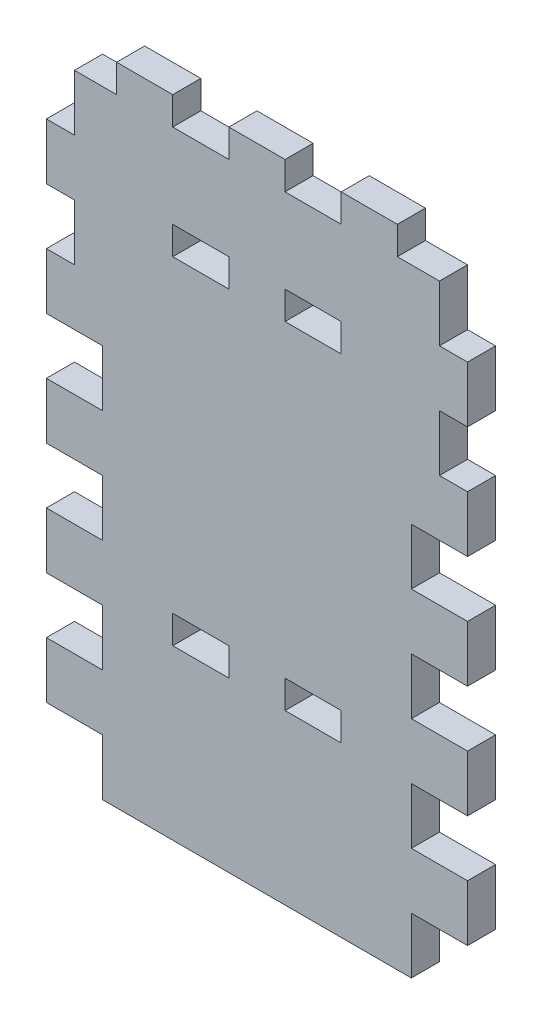
SolidWorks part; units mm, degrees
ref_plane "Front Plane" through (0, 0, 0) normal (0, 0, 1) x (1, 0, 0)
ref_plane "Top Plane" through (0, 0, 0) normal (0, 1, 0) x (1, 0, 0)
ref_plane "Right Plane" through (0, 0, 0) normal (1, 0, 0) x (0, 0, -1)
sketch "Sketch1" plane through (0, 0, 0) normal (0, 0, 1) x (1, 0, 0)
  line L1 (0, 0) -> (95.25, 0)
  line L2 (0, 0) -> (0, 177.8)
  line L3 (0, 177.8) -> (95.25, 177.8)
  line L4 (95.25, 0) -> (95.25, 177.8)
  dimension "D1" = 95.25
  dimension "D2" = 177.8
extrude "Boss-Extrude1" add sketch "Sketch1" along normal blind 6.35 contours L3 L4 L1 L2
sketch "Sketch2" plane through (0, 0, 6.35) normal (0, 0, 1) x (1, 0, 0)
  line L0 (0, 0) -> (0, 177.8) construction
  line L1 (0, 12.7) -> (12.7, 12.7)
  line L2 (0, 12.7) -> (0, 0)
  line L3 (0, 0) -> (12.7, 0)
  line L4 (12.7, 12.7) -> (12.7, 0)
  line L5 (0, 0) -> (95.25, 0) construction
  line L6 (95.25, 0) -> (95.25, 177.8) construction
  line L7 (95.25, 12.7) -> (82.55, 12.7)
  line L8 (95.25, 12.7) -> (95.25, 0)
  line L9 (95.25, 0) -> (82.55, 0)
  line L10 (82.55, 12.7) -> (82.55, 0)
  dimension "D1" = 12.7
  dimension "D2" = 12.7
extrude "Cut-Extrude1" cut sketch "Sketch2" against normal through all
pattern_linear "LPattern1" count 4 spacing 25.4 along (0, 1, 0) of "Cut-Extrude1"
sketch "Sketch3" plane through (0, 0, 6.35) normal (0, 0, 1) x (1, 0, 0)
  line L0 (47.625, 0) -> (47.625, 41.275) construction
  line L1 (28.575, 44.45) -> (41.275, 44.45)
  line L2 (28.575, 44.45) -> (28.575, 38.1)
  line L3 (28.575, 38.1) -> (41.275, 38.1)
  line L4 (41.275, 44.45) -> (41.275, 38.1)
  line L5 (53.975, 44.45) -> (66.675, 44.45)
  line L6 (53.975, 44.45) -> (53.975, 38.1)
  line L7 (53.975, 38.1) -> (66.675, 38.1)
  line L8 (66.675, 44.45) -> (66.675, 38.1)
  line L9 (12.7, 0) -> (82.55, 0) construction
  line L10 (41.275, 41.275) -> (53.975, 41.275) construction
  dimension "D1" = 12.7
  dimension "D2" = 6.35
  dimension "D3" = 38.1
extrude "Cut-Extrude2" cut sketch "Sketch3" against normal through all
sketch "Sketch4" plane through (0, 0, 6.35) normal (0, 0, 1) x (1, 0, 0)
  line L0 (44.45, 163.25) -> (44.45, 99.25) construction
  line L1 (0, 88.9) -> (0, 177.8) construction
  line L2 (12.7, 0) -> (82.55, 0) construction
  line L4 (44.45, 163.25) -> (57.15, 163.25) construction
  line L5 (44.45, 163.25) -> (44.45, 99.25) construction
  line L6 (44.45, 99.25) -> (57.15, 99.25) construction
  line L7 (57.15, 163.25) -> (57.15, 99.25) construction
  circle A0 centre (44.45, 163.25) radius 1.75
  circle A1 centre (44.45, 99.25) radius 1.75
  circle A2 centre (57.15, 163.25) radius 1.75
  circle A3 centre (57.15, 99.25) radius 1.75
  dimension "D4" = 3.5
  dimension "D1" = 44.45
  dimension "D2" = 64
  dimension "D3" = 99.25
  dimension "D5" = 12.7
sketch "Sketch5" plane through (0, 0, 6.35) normal (0, 0, 1) x (1, 0, 0)
  line L0 (0, 88.9) -> (0, 177.8) construction
  line L1 (0, 101.6) -> (6.35, 101.6)
  line L2 (0, 101.6) -> (0, 114.3)
  line L3 (0, 114.3) -> (6.35, 114.3)
  line L4 (6.35, 101.6) -> (6.35, 114.3)
  line L5 (95.25, 88.9) -> (95.25, 177.8) construction
  line L6 (95.25, 114.3) -> (88.9, 114.3)
  line L7 (95.25, 114.3) -> (95.25, 101.6)
  line L8 (95.25, 101.6) -> (88.9, 101.6)
  line L9 (88.9, 114.3) -> (88.9, 101.6)
  line L10 (12.7, 76.2) -> (12.7, 88.9) construction
  line L11 (12.7, 88.9) -> (0, 88.9) construction
  dimension "D1" = 12.7
  dimension "D2" = 6.35
extrude "Cut-Extrude4" cut sketch "Sketch5" against normal through all
pattern_linear "LPattern2" count 4 spacing 25.4 along (0, 1, 0) of "Cut-Extrude4"
sketch "Sketch6" plane through (0, 0, 6.35) normal (0, 0, 1) x (1, 0, 0)
  line L1 (0, 177.8) -> (95.25, 177.8)
  line L2 (0, 177.8) -> (0, 139.7)
  line L3 (0, 139.7) -> (95.25, 139.7)
  line L4 (95.25, 177.8) -> (95.25, 139.7)
extrude "Cut-Extrude5" cut sketch "Sketch6" against normal through all
sketch "Sketch7" plane through (0, 139.7, 0) normal (0, 1, 0) x (1, 0, 0)
  line L0 (6.35, 0) -> (88.9, 0) construction
  line L1 (41.275, 0) -> (53.975, 0)
  line L2 (41.275, 0) -> (41.275, -6.35)
  line L3 (41.275, -6.35) -> (53.975, -6.35)
  line L4 (53.975, 0) -> (53.975, -6.35)
  line L5 (6.35, -6.35) -> (88.9, -6.35) construction
  point P8 (47.625, -6.35)
  dimension "D1" = 12.7
extrude "Boss-Extrude2" add sketch "Sketch7" along normal blind 6.35
pattern_linear "LPattern3" count 2 spacing 25.4 along (1, 0, 0) count 2 spacing 25.4 along (-1, 0, 0) of "Boss-Extrude2"
pattern_linear "LPattern4" count 2 spacing 76.2 along (0, 1, 0) of "Cut-Extrude2"
